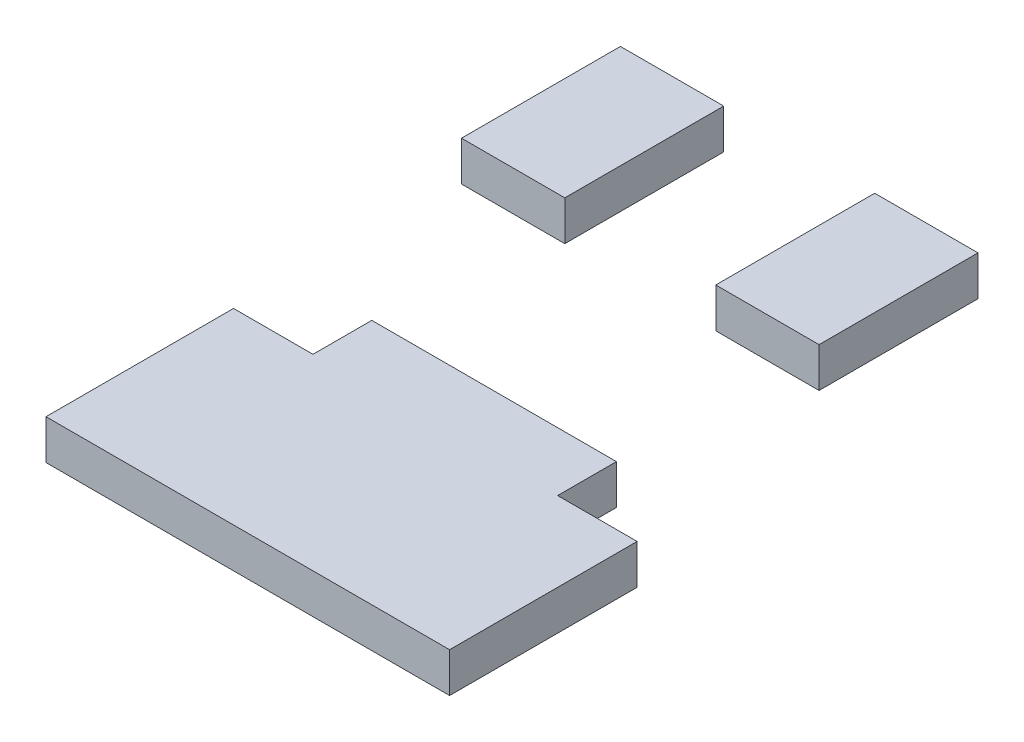
SolidWorks part; units mm, degrees
ref_plane "Front" through (0, 0, 0) normal (0, 0, 1) x (1, 0, 0)
ref_plane "Top" through (0, 0, 0) normal (0, 1, 0) x (1, 0, 0)
ref_plane "Right" through (0, 0, 0) normal (1, 0, 0) x (0, 0, -1)
sketch "Sketch1" plane through (0, 0, 0) normal (0, 1, 0) x (1, 0, 0)
  line L0 (0, 55.0879) -> (0, -55.3731) construction
  line L1 (-15.2897, -6.5269) -> (-25.2897, -6.5269)
  line L2 (-35, 36.3731) -> (35, 36.3731) construction
  line L3 (-7, 55.3731) -> (-7, -44.6269) construction
  line L4 (-15.2897, 0.8731) -> (15.5, 0.8731)
  line L5 (-29.5, 26.3731) -> (-16.5, 26.3731)
  line L6 (15.5, 46.3731) -> (2.5, 26.3731) construction
  line L7 (15.5, 26.3731) -> (2.5, 46.3731) construction
  line L8 (-29.5, 26.3731) -> (-29.5, 46.3731)
  line L9 (-29.5, 46.3731) -> (-16.5, 46.3731)
  line L10 (-25.2897, -6.5269) -> (-25.2897, -30.1269)
  line L11 (-16.5, 26.3731) -> (-16.5, 46.3731)
  line L12 (-15.2897, -6.5269) -> (-15.2897, 0.8731)
  line L13 (15.5, 0.8731) -> (15.5, -6.5269)
  line L14 (15.5, -6.5269) -> (25.5, -6.5269)
  line L15 (25.5, -6.5269) -> (25.5, -30.1269)
  line L16 (25.5, -30.1269) -> (-25.2897, -30.1269)
  line L17 (-29.5, 26.3731) -> (-16.5, 46.3731) construction
  line L18 (-29.5, 46.3731) -> (-16.5, 26.3731) construction
  line L19 (2.5, 26.3731) -> (2.5, 46.3731)
  line L20 (15.5, 46.3731) -> (2.5, 46.3731)
  line L21 (15.5, 26.3731) -> (15.5, 46.3731)
  line L22 (15.5, 26.3731) -> (2.5, 26.3731)
  point P0 (0, -14.6269)
  point P7 (-23, 36.3731)
  point P24 (9, 36.3731)
extrude "Boss-Extrude1" add sketch "Sketch1" along normal blind 5
